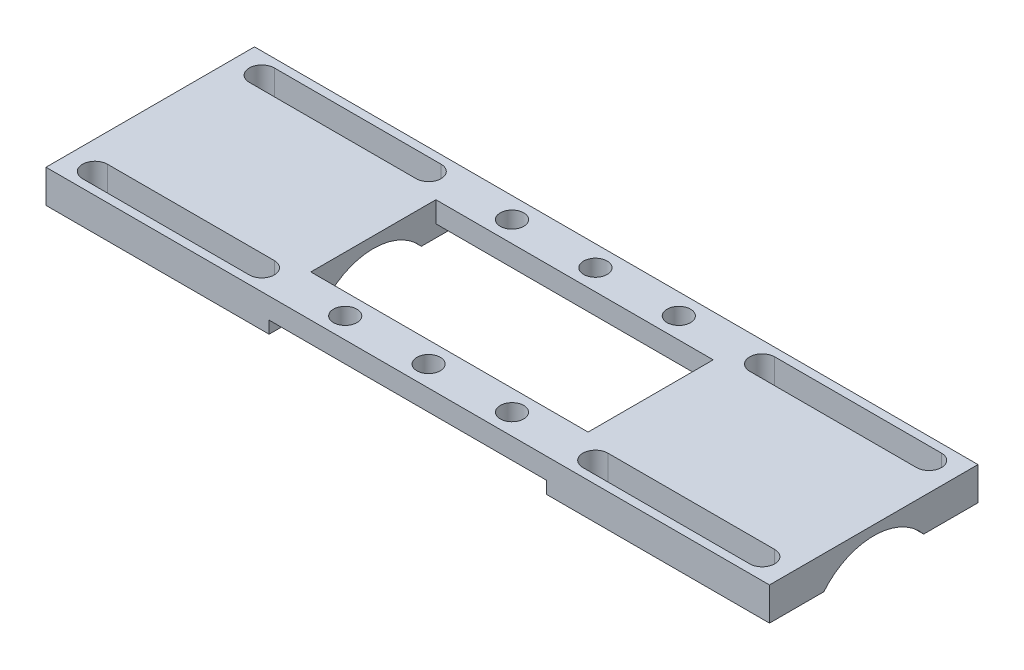
SolidWorks part; units mm, degrees
ref_plane "Front Plane" through (0, 0, 0) normal (0, 0, 1) x (1, 0, 0)
ref_plane "Top Plane" through (0, 0, 0) normal (0, 1, 0) x (1, 0, 0)
ref_plane "Right Plane" through (0, 0, 0) normal (1, 0, 0) x (0, 0, -1)
sketch "Sketch3" plane through (0, 0, 0) normal (0, 1, 0) x (1, 0, 0)
  line L0 (32, 16) -> (64, 16) construction
  line L1 (69.4, 20) -> (26.6, 20)
  line L2 (69.4, 20) -> (69.4, -20)
  line L3 (69.4, -20) -> (26.6, -20)
  line L4 (26.6, 20) -> (26.6, -20)
  line L5 (32, 18.4) -> (64, 18.4)
  line L6 (32, 13.6) -> (64, 13.6)
  line L7 (26.6, 0) -> (69.4, 0) construction
  line L10 (32, -16) -> (64, -16) construction
  line L11 (32, -18.4) -> (64, -18.4)
  line L12 (32, -13.6) -> (64, -13.6)
  line L13 (0, 0) -> (0, 20) construction
  arc A0 (32, 18.4) -> (32, 13.6) centre (32, 16) ccw
  arc A1 (64, 13.6) -> (64, 18.4) centre (64, 16) ccw
  arc A4 (32, -18.4) -> (32, -13.6) centre (32, -16) cw
  arc A5 (64, -13.6) -> (64, -18.4) centre (64, -16) cw
  point P4 (69.4, 0)
  point P8 (48, 16)
  point P17 (48, -16)
  point P24 (48, 0)
  dimension "D3" = 4.8
  dimension "D1" = 40
  dimension "D2" = 26.6
  dimension "D4" = 32
  dimension "D5" = 32
  dimension "D6" = 32
extrude "Boss-Extrude1" add sketch "Sketch3" along normal blind 6.35
sketch "Sketch4" plane through (69.4, 0, 0) normal (1, 0, 0) x (0, 0, -1)
  line L0 (-20, 0) -> (20, 0) construction
  circle A0 centre (0, -7.874) radius 12.4
  dimension "D1" = 24.8
  dimension "D2" = 7.874
extrude "Cut-Extrude1" cut sketch "Sketch4" against normal offset from surface (12.8 mm away) 56.6 up to plane "Right Plane"
sketch "Sketch5" plane through (56.6, 0, 0) normal (1, 0, 0) x (0, 0, -1)
  circle A0 centre (0, -7.874) radius 12.115
  dimension "D1" = 24.23
extrude "Cut-Extrude2" cut sketch "Sketch5" against normal through all
mirror "Mirror2" about plane through (0, 0, 0) normal (1, 0, 0) of bodies 103
sketch "Sketch6" plane through (26.6, 0, 0) normal (-1, 0, 0) x (0, 0, 1)
  line L1 (-20, 6.35) -> (-12, 6.35)
  line L2 (-20, 6.35) -> (-20, 2.35)
  line L3 (-20, 2.35) -> (-12, 2.35)
  line L4 (-12, 6.35) -> (-12, 2.35)
  line L5 (20, 6.35) -> (12, 6.35)
  line L6 (20, 6.35) -> (20, 2.35)
  line L7 (20, 2.35) -> (12, 2.35)
  line L8 (12, 6.35) -> (12, 2.35)
  dimension "D1" = 4
  dimension "D2" = 8
extrude "Boss-Extrude2" add sketch "Sketch6" along normal up to surface (53.2 mm away) up to face at (-26.6, 2.8235, 0)
sketch "Sketch7" plane through (0, 6.35, 0) normal (0, 1, 0) x (1, 0, 0)
  circle A0 centre (-16, 16) radius 2.25
  dimension "D2" = 4.5
  dimension "D1" = 16
  dimension "D3" = 16
extrude "Cut-Extrude3" cut sketch "Sketch7" against normal up to next (4 mm away)
pattern_linear "LPattern1" count 3 spacing 16 along (1, 0, 0) count 2 spacing 32 along (0, 0, 1) of "Cut-Extrude3"
